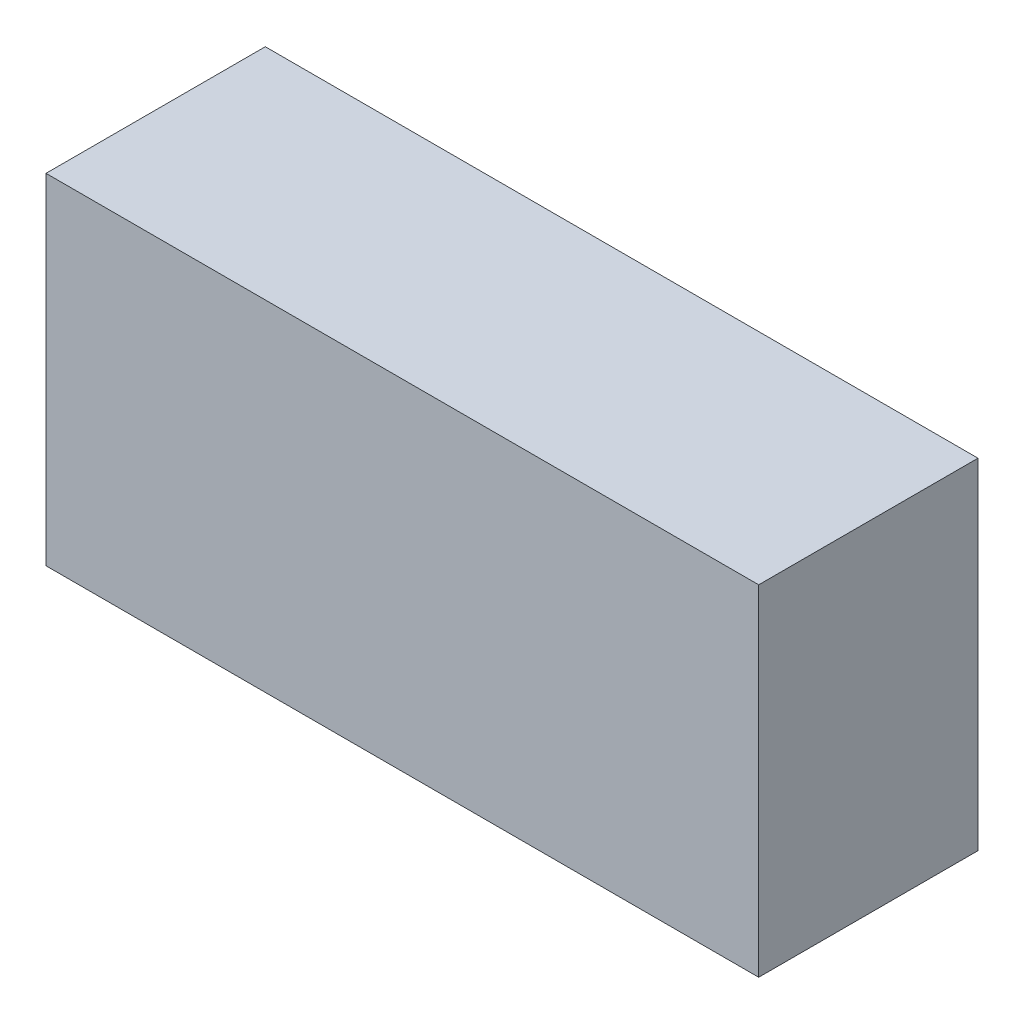
SolidWorks part; units mm, degrees
ref_plane "Спереди" through (0, 0, 0) normal (0, 0, 1) x (1, 0, 0)
ref_plane "Сверху" through (0, 0, 0) normal (0, 1, 0) x (1, 0, 0)
ref_plane "Справа" through (0, 0, 0) normal (1, 0, 0) x (0, 0, -1)
sketch "Эскиз1" plane through (0, 0, 0) normal (0, 1, 0) x (1, 0, 0)
  line L1 (-9.75, 3) -> (9.75, 3)
  line L2 (-9.75, 3) -> (-9.75, -3)
  line L3 (-9.75, -3) -> (9.75, -3)
  line L4 (9.75, 3) -> (9.75, -3)
  line L5 (-9.75, 3) -> (9.75, -3) construction
  line L6 (-9.75, -3) -> (9.75, 3) construction
  point P0 (0, 0)
  dimension "D1" = 19.5
  dimension "D2" = 6
extrude "Бобышка-Вытянуть1" add sketch "Эскиз1" along normal blind 9.3
sketch "Эскиз2" plane through (0, 0, 0) normal (0, -1, 0) x (1, 0, 0)
  line L0 (9.75, -3) -> (-9.75, -3) construction
  line L1 (-7.92, -1.2) -> (-7.32, -1.2)
  line L2 (-7.92, -1.2) -> (-7.92, -1.5)
  line L3 (-7.92, -1.5) -> (-7.32, -1.5)
  line L4 (-7.32, -1.2) -> (-7.32, -1.5)
  line L5 (-7.92, -1.2) -> (-7.32, -1.5) construction
  line L6 (-7.92, -1.5) -> (-7.32, -1.2) construction
  line L7 (-9.75, -3) -> (-9.75, 3) construction
  line L8 (-7.9208, -1.1995) -> (-7.3208, -1.1995)
  line L9 (-7.9208, -1.1995) -> (-7.9208, -1.4995)
  line L10 (-7.9208, -1.4995) -> (-7.3208, -1.4995)
  line L11 (-7.3208, -1.1995) -> (-7.3208, -1.4995)
  line L13 (-5.38, -1.2) -> (-4.78, -1.2)
  line L14 (-5.38, -1.2) -> (-5.38, -1.5)
  line L15 (-5.38, -1.5) -> (-4.78, -1.5)
  line L16 (-4.78, -1.2) -> (-4.78, -1.5)
  line L17 (-5.38, -1.2) -> (-4.78, -1.5) construction
  line L18 (-5.38, -1.5) -> (-4.78, -1.2) construction
  line L19 (-0.3, -1.2) -> (0.3, -1.2)
  line L20 (-0.3, -1.2) -> (-0.3, -1.5)
  line L21 (-0.3, -1.5) -> (0.3, -1.5)
  line L22 (0.3, -1.2) -> (0.3, -1.5)
  line L23 (-0.3, -1.2) -> (0.3, -1.5) construction
  line L24 (-0.3, -1.5) -> (0.3, -1.2) construction
  line L29 (2.24, -1.2) -> (2.84, -1.5) construction
  line L30 (2.24, -1.5) -> (2.84, -1.2) construction
  line L31 (4.78, -1.2) -> (5.38, -1.2)
  line L32 (4.78, -1.2) -> (4.78, -1.5)
  line L33 (4.78, -1.5) -> (5.38, -1.5)
  line L34 (5.38, -1.2) -> (5.38, -1.5)
  line L35 (4.78, -1.2) -> (5.38, -1.5) construction
  line L36 (4.78, -1.5) -> (5.38, -1.2) construction
  point P0 (-7.62, -1.35)
  point P9 (0, -1.35)
  point P17 (-5.08, -1.35)
  point P23 (2.54, -1.35)
  point P28 (5.08, -1.35)
  point P33 (0, 0)
  point P34 (0, 0)
  point P35 (2.54, -1.35)
  dimension "D1" = 1.65
  dimension "D2" = 2.13
  dimension "D3" = 0.6
  dimension "D4" = 0.3
  dimension "D5" = 0.6
  dimension "D6" = 0.6
  dimension "D7" = 0.6
  dimension "D8" = 0.6
  dimension "D9" = 0.3
  dimension "D10" = 0.3
  dimension "D11" = 0.3
  dimension "D12" = 0.3
  dimension "D13" = 1.65
  dimension "D14" = 1.65
  dimension "D15" = 1.65
  dimension "D16" = 1.65
  dimension "D17" = 2.54
  dimension "D18" = 5.08
  dimension "D19" = 2.54
  dimension "D20" = 2.54
extrude "Бобышка-Вытянуть2" add sketch "Эскиз2" along normal blind 3
sketch "Эскиз3" plane through (0, 9.3, 0) normal (0, 1, 0) x (1, 0, 0)
  text T0 "DC Converter" font "Century Gothic" height in points 10
extrude "Бобышка-Вытянуть3" add sketch "Эскиз3" against normal blind 0.2
